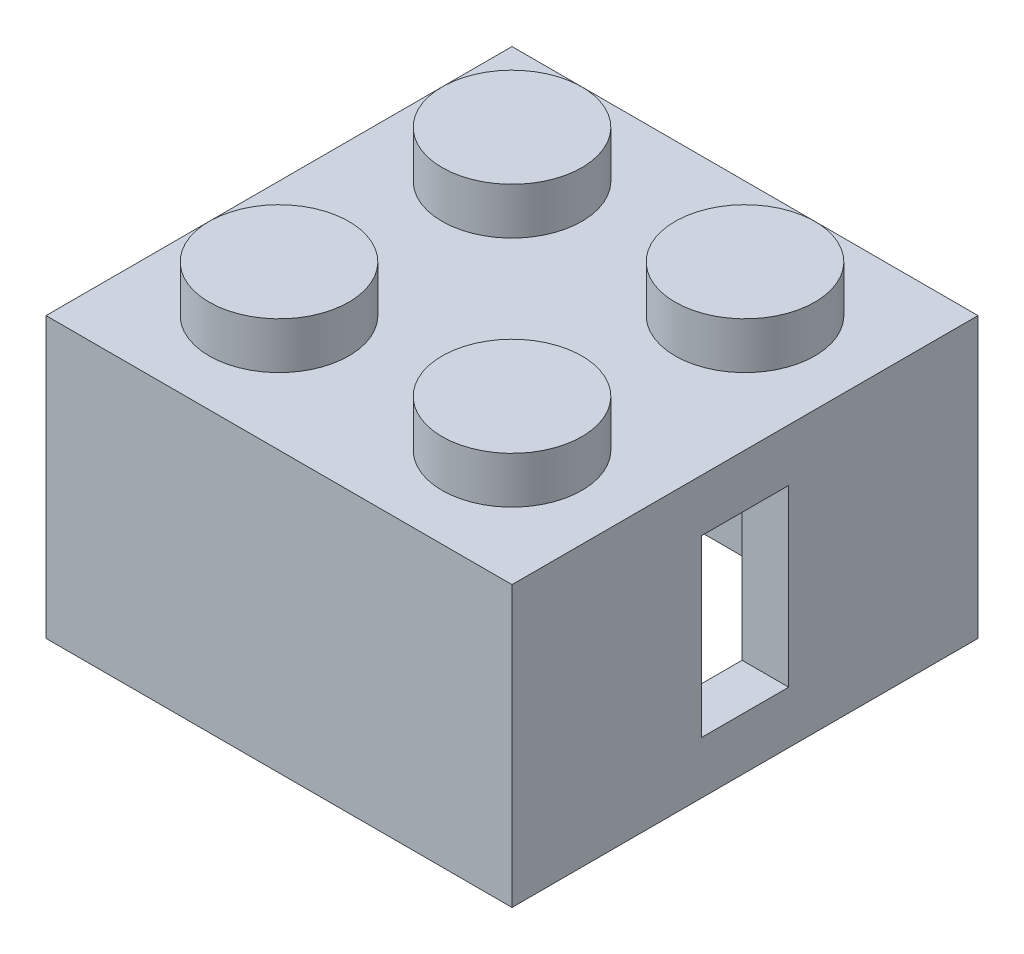
SolidWorks part; units mm, degrees
ref_plane "Front Plane" through (0, 0, 0) normal (0, 0, 1) x (1, 0, 0)
ref_plane "Top Plane" through (0, 0, 0) normal (0, 1, 0) x (1, 0, 0)
ref_plane "Right Plane" through (0, 0, 0) normal (1, 0, 0) x (0, 0, -1)
sketch "Sketch1" plane through (0, 0, 0) normal (0, 1, 0) x (1, 0, 0)
  line L0 (14.4, 1.6) -> (14.4, 14.4)
  line L1 (0, 0) -> (16, 0)
  line L2 (0, 0) -> (0, 16)
  line L3 (0, 16) -> (16, 16)
  line L4 (16, 0) -> (16, 16)
  line L5 (1.6, 14.4) -> (14.4, 14.4)
  line L6 (1.6, 1.6) -> (1.6, 14.4)
  line L7 (1.6, 1.6) -> (14.4, 1.6)
  dimension "D1" = 16
  dimension "D2" = 1.6
extrude "Boss-Extrude1" add sketch "Sketch1" along normal blind 8
sketch "Sketch2" plane through (0, 8, 0) normal (0, 1, 0) x (1, 0, 0)
  line L0 (0, 0) -> (16, 0) construction
  line L1 (0, 16) -> (0, 0) construction
  line L2 (16, 16) -> (0, 16) construction
  line L3 (16, 0) -> (16, 16) construction
  line L4 (0, 0) -> (16, 0)
  line L5 (0, 16) -> (0, 0)
  line L6 (16, 16) -> (0, 16)
  line L7 (16, 0) -> (16, 16)
extrude "Boss-Extrude2" add sketch "Sketch2" along normal blind 1.6
sketch "Sketch3" plane through (0, 9.6, 0) normal (0, 1, 0) x (1, 0, 0)
  line L0 (4, 4) -> (4, 12) construction
  line L1 (4, 12) -> (12, 12) construction
  line L2 (12, 12) -> (12, 4) construction
  line L3 (12, 4) -> (4, 4) construction
  line L4 (12, 12) -> (12, 16) construction
  line L5 (12, 12) -> (16, 12) construction
  line L6 (4, 4) -> (4, 0) construction
  line L7 (4, 4) -> (0, 4) construction
  line L8 (0, 16) -> (0, 0)
  line L9 (0, 0) -> (16, 0)
  line L10 (16, 0) -> (16, 16)
  line L11 (16, 16) -> (0, 16)
  line L12 (0, 16) -> (0, 0)
  line L13 (0, 0) -> (16, 0)
  line L14 (16, 0) -> (16, 16)
  line L15 (16, 16) -> (0, 16)
  circle A0 centre (4, 12) radius 2.4
  circle A1 centre (12, 12) radius 2.4
  circle A2 centre (4, 4) radius 2.4
  circle A3 centre (12, 4) radius 2.4
  dimension "D2" = 4.8
  dimension "D1" = 8
  dimension "D3" = 0
extrude "Boss-Extrude3" add sketch "Sketch3" along normal blind 1.6 contours A3 | A2 | A0 | A1
sketch "Sketch4" plane through (0, 0, 0) normal (-1, 0, 0) x (0, 0, 1)
  line L0 (-8, 9.6) -> (-8, 0) construction
  line L1 (-16, 9.6) -> (0, 9.6) construction
  line L2 (-16, 0) -> (0, 0) construction
  line L3 (-16, 4.8) -> (0, 4.8) construction
  line L4 (-16, 9.6) -> (-16, 0) construction
  line L5 (0, 9.6) -> (0, 0) construction
  circle A0 centre (-8, 4.8) radius 3.25
  point P14 (-8, 4.8)
  point P16 (-8, 4.8)
  dimension "D1" = 6.5
extrude "Cut-Extrude1" cut sketch "Sketch4" against normal up to surface (1.6 mm away) up to face at (1.6, 4, -8)
sketch "Sketch7" plane through (16, 0, 0) normal (1, 0, 0) x (0, 0, -1)
  line L0 (6.5, 4.8) -> (9.5, 4.8) construction
  line L1 (8, 1.8) -> (8, 7.8) construction
  line L2 (6.5, 1.8) -> (9.5, 1.8)
  line L3 (6.5, 1.8) -> (6.5, 7.8)
  line L4 (6.5, 7.8) -> (9.5, 7.8)
  line L5 (9.5, 1.8) -> (9.5, 7.8)
  circle A0 centre (8, 4.8) radius 3.25 construction
  circle A1 centre (8, 4.8) radius 3.25 construction
  point P6 (8, 4.8)
  point P10 (0, 0)
  point P13 (8, 4.8)
  dimension "D1" = 3
  dimension "D2" = 6
extrude "Cut-Extrude2" cut sketch "Sketch7" against normal blind 1.6
